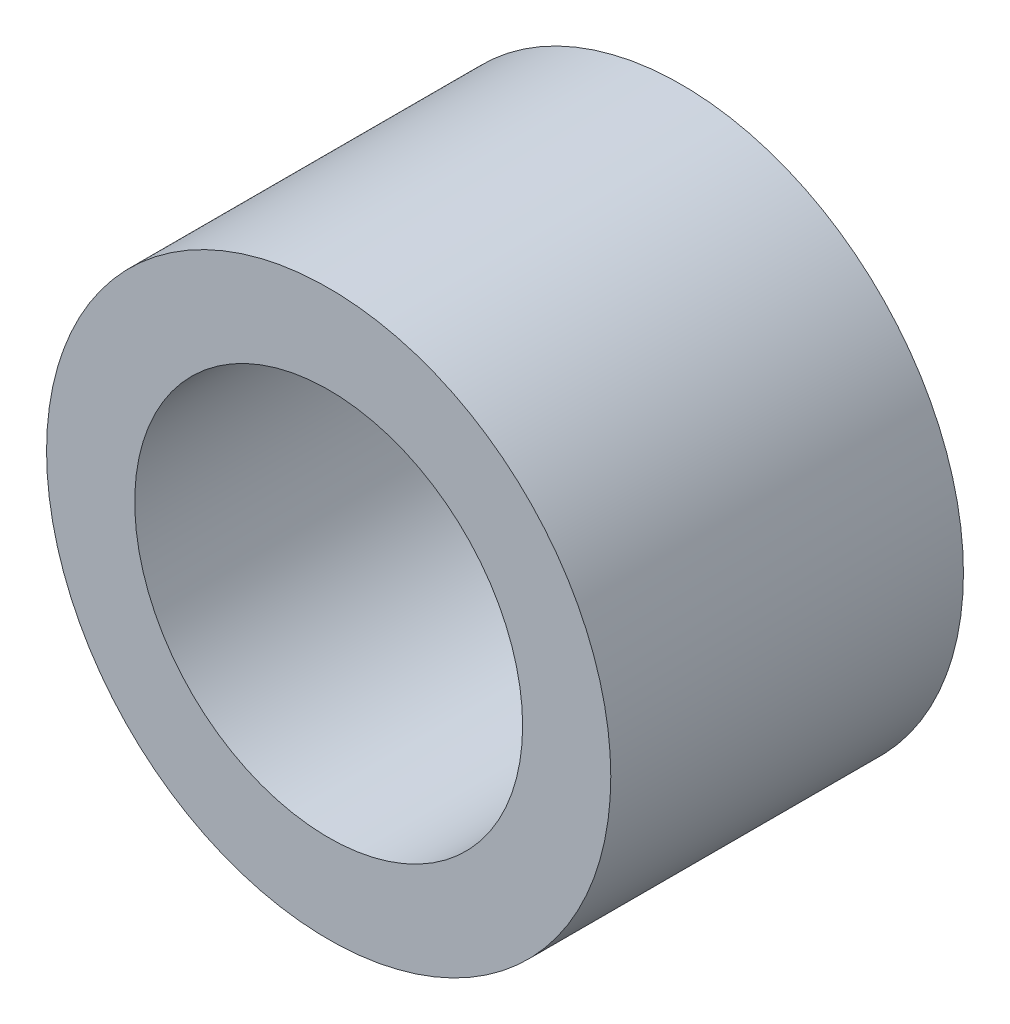
SolidWorks part; units mm, degrees
ref_plane "正面" through (0, 0, 0) normal (0, 0, 1) x (1, 0, 0)
ref_plane "平面" through (0, 0, 0) normal (0, 1, 0) x (1, 0, 0)
ref_plane "右側面" through (0, 0, 0) normal (1, 0, 0) x (0, 0, -1)
sketch "ｽｹｯﾁ1" plane through (0, 0, 0) normal (0, 0, 1) x (1, 0, 0)
  circle A0 centre (0, 0) radius 2.75
  circle A1 centre (0, 0) radius 4
  dimension "D1" = 5.5
  dimension "D2" = 8
extrude "ﾎﾞｽ - 押し出し1" add sketch "ｽｹｯﾁ1" along normal blind 5
